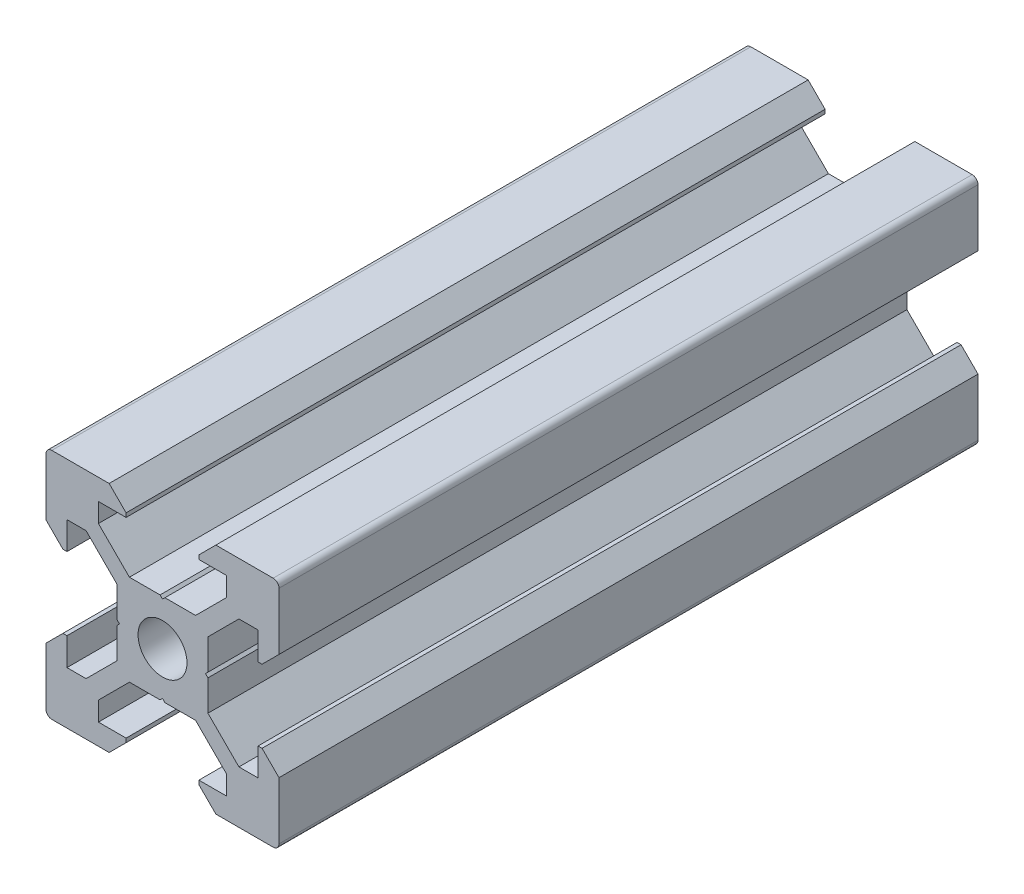
SolidWorks part; units mm, degrees
material "6061-T6 (SS)"
ref_plane "Front Plane" through (0, 0, 0) normal (0, 0, 1) x (1, 0, 0)
ref_plane "Top Plane" through (0, 0, 0) normal (0, 1, 0) x (1, 0, 0)
ref_plane "Right Plane" through (0, 0, 0) normal (1, 0, 0) x (0, 0, -1)
sketch "Sketch1" plane through (0, 0, 0) normal (0, 0, 1) x (1, 0, 0)
  line L1 (9.5, -10) -> (-9.5, -10)
  line L2 (10, -9.5) -> (10, 9.5)
  line L3 (9.5, 10) -> (-9.5, 10)
  line L4 (-10, -9.5) -> (-10, 9.5)
  line L5 (10, -10) -> (-10, 10) construction
  line L6 (10, 10) -> (-10, -10) construction
  circle A0 centre (0, 0) radius 2.1
  arc A1 (-9.5, 10) -> (-10, 9.5) centre (-9.5, 9.5) ccw
  arc A2 (10, 9.5) -> (9.5, 10) centre (9.5, 9.5) ccw
  arc A3 (9.5, -10) -> (10, -9.5) centre (9.5, -9.5) ccw
  arc A4 (-9.5, -10) -> (-10, -9.5) centre (-9.5, -9.5) cw
  point P0 (0, 0)
  line B0 (0, 0) -> (0, 10) construction
  line B1 (0, 3.69) -> (-0.21, 3.9)
  line B2 (-0.21, 3.9) -> (-2.8393, 3.9)
  line B3 (-2.8393, 3.9) -> (-5.5, 6.5607)
  line B4 (-5.5, 6.5607) -> (-5.5, 8.2)
  line B5 (-5.5, 8.2) -> (-3.125, 8.2)
  line B6 (-3.125, 8.2) -> (-3.125, 8.545)
  line B7 (-3.125, 8.545) -> (-4.58, 10)
  line B8 (-4.58, 10) -> (4.58, 10)
  line B9 (0, 0) -> (-5.9132, 5.9132) construction
  line B10 (3.125, 8.545) -> (4.58, 10)
  line B11 (3.125, 8.2) -> (3.125, 8.545)
  line B12 (5.5, 8.2) -> (3.125, 8.2)
  line B13 (5.5, 6.5607) -> (5.5, 8.2)
  line B14 (2.8393, 3.9) -> (5.5, 6.5607)
  line B15 (0.21, 3.9) -> (2.8393, 3.9)
  line B16 (0, 3.69) -> (0.21, 3.9)
  line B17 (0, 0) -> (-10, 0) construction
  line B18 (-3.69, 0) -> (-3.9, -0.21)
  line B19 (-3.9, -0.21) -> (-3.9, -2.8393)
  line B20 (-3.9, -2.8393) -> (-6.5607, -5.5)
  line B21 (-6.5607, -5.5) -> (-8.2, -5.5)
  line B22 (-8.2, -5.5) -> (-8.2, -3.125)
  line B23 (-8.2, -3.125) -> (-8.545, -3.125)
  line B24 (-8.545, -3.125) -> (-10, -4.58)
  line B25 (-10, -4.58) -> (-10, 4.58)
  line B26 (0, 0) -> (-5.9132, -5.9132) construction
  line B27 (-8.545, 3.125) -> (-10, 4.58)
  line B28 (-8.2, 3.125) -> (-8.545, 3.125)
  line B29 (-8.2, 5.5) -> (-8.2, 3.125)
  line B30 (-6.5607, 5.5) -> (-8.2, 5.5)
  line B31 (-3.9, 2.8393) -> (-6.5607, 5.5)
  line B32 (-3.9, 0.21) -> (-3.9, 2.8393)
  line B33 (-3.69, 0) -> (-3.9, 0.21)
  line B34 (0, 0) -> (0, -10) construction
  line B35 (0, -3.69) -> (0.21, -3.9)
  line B36 (0.21, -3.9) -> (2.8393, -3.9)
  line B37 (2.8393, -3.9) -> (5.5, -6.5607)
  line B38 (5.5, -6.5607) -> (5.5, -8.2)
  line B39 (5.5, -8.2) -> (3.125, -8.2)
  line B40 (3.125, -8.2) -> (3.125, -8.545)
  line B41 (3.125, -8.545) -> (4.58, -10)
  line B42 (4.58, -10) -> (-4.58, -10)
  line B43 (0, 0) -> (5.9132, -5.9132) construction
  line B44 (-3.125, -8.545) -> (-4.58, -10)
  line B45 (-3.125, -8.2) -> (-3.125, -8.545)
  line B46 (-5.5, -8.2) -> (-3.125, -8.2)
  line B47 (-5.5, -6.5607) -> (-5.5, -8.2)
  line B48 (-2.8393, -3.9) -> (-5.5, -6.5607)
  line B49 (-0.21, -3.9) -> (-2.8393, -3.9)
  line B50 (0, -3.69) -> (-0.21, -3.9)
  line B51 (0, 0) -> (10, 0) construction
  line B52 (3.69, 0) -> (3.9, 0.21)
  line B53 (3.9, 0.21) -> (3.9, 2.8393)
  line B54 (3.9, 2.8393) -> (6.5607, 5.5)
  line B55 (6.5607, 5.5) -> (8.2, 5.5)
  line B56 (8.2, 5.5) -> (8.2, 3.125)
  line B57 (8.2, 3.125) -> (8.545, 3.125)
  line B58 (8.545, 3.125) -> (10, 4.58)
  line B59 (10, 4.58) -> (10, -4.58)
  line B60 (0, 0) -> (5.9132, 5.9132) construction
  line B61 (8.545, -3.125) -> (10, -4.58)
  line B62 (8.2, -3.125) -> (8.545, -3.125)
  line B63 (8.2, -5.5) -> (8.2, -3.125)
  line B64 (6.5607, -5.5) -> (8.2, -5.5)
  line B65 (3.9, -2.8393) -> (6.5607, -5.5)
  line B66 (3.9, -0.21) -> (3.9, -2.8393)
  line B67 (3.69, 0) -> (3.9, -0.21)
  dimension "D1" = 4.2
  dimension "D3" = 0.5
  dimension "D2" = 20
sketch_block_instance "V Slot 1-4"
sketch_block "V Slot 1" parameters "D1"=10, "D2"=11, "D3"=4.3, "D4"=1.8, "D5"=0.21, "D6"=45, "D7"=9.16, "D8"=1.5, "D9"=6.25
sketch_block_instance "V Slot 1-5"
sketch_block_instance "V Slot 1-6"
sketch_block_instance "V Slot 1-7"
extrude "Boss-Extrude1" add sketch "Sketch1" along normal blind 60 contours B67 B52 B53 B54 B55 B56 B57 B58 L2 A2 L3 B10 B11 B12 B13 B14 B15 B16 B1 B2 B3 B4 B5 B6 B7 A1 L4 B27 B28 B29 B30 B31 B32 B33 B18 B19 B20 B21 B22 B23 B24 A4 L1 B44 B45 B46 B47 B48 B49
